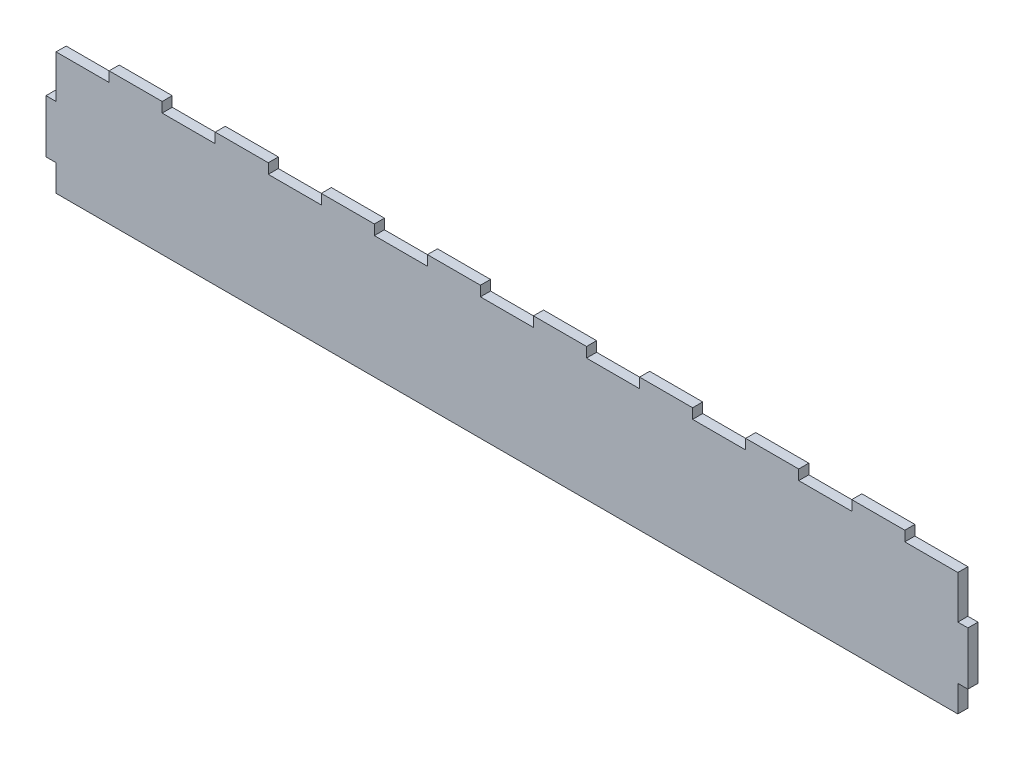
SolidWorks part; units mm, degrees
material "1060 Alloy"
ref_plane "Front Plane" through (0, 0, 0) normal (0, 0, 1) x (1, 0, 0)
ref_plane "Top Plane" through (0, 0, 0) normal (0, 1, 0) x (1, 0, 0)
ref_plane "Right Plane" through (0, 0, 0) normal (1, 0, 0) x (0, 0, -1)
sketch "Sketch2" plane through (0, 0, 0) normal (0, 0, 1) x (1, 0, 0)
  line L0 (0, 101.6) -> (0, 127)
  line L1 (0, 0) -> (431.8, 0)
  line L2 (0, 0) -> (0, 25.4)
  line L3 (0, 127) -> (431.8, 127)
  line L4 (431.8, 50.8) -> (431.8, 76.2)
  line L5 (0, 101.6) -> (-4.826, 101.6)
  line L6 (50.8, 122.174) -> (76.2, 122.174)
  line L7 (0, 76.2) -> (-4.826, 76.2)
  line L8 (-4.826, 101.6) -> (-4.826, 76.2)
  line L9 (0, 50.8) -> (-4.826, 50.8)
  line L10 (406.4, 122.174) -> (431.8, 122.174)
  line L11 (0, 25.4) -> (-4.826, 25.4)
  line L12 (-4.826, 50.8) -> (-4.826, 25.4)
  line L13 (0, 50.8) -> (0, 76.2)
  line L14 (215.9, 127) -> (215.9, 0) construction
  line L15 (406.4, 127) -> (406.4, 122.174)
  line L16 (0, 127) -> (25.4, 127)
  line L17 (0, 127) -> (0, 122.174)
  line L18 (0, 122.174) -> (25.4, 122.174)
  line L19 (25.4, 127) -> (25.4, 122.174)
  line L20 (50.8, 127) -> (50.8, 122.174)
  line L21 (76.2, 127) -> (76.2, 122.174)
  line L22 (101.6, 122.174) -> (127, 122.174)
  line L23 (101.6, 127) -> (101.6, 122.174)
  line L24 (127, 127) -> (127, 122.174)
  line L25 (152.4, 122.174) -> (177.8, 122.174)
  line L26 (152.4, 127) -> (152.4, 122.174)
  line L27 (177.8, 127) -> (177.8, 122.174)
  line L28 (203.2, 122.174) -> (228.6, 122.174)
  line L29 (203.2, 127) -> (203.2, 122.174)
  line L30 (228.6, 127) -> (228.6, 122.174)
  line L31 (254, 122.174) -> (279.4, 122.174)
  line L32 (254, 127) -> (254, 122.174)
  line L33 (279.4, 127) -> (279.4, 122.174)
  line L34 (304.8, 122.174) -> (330.2, 122.174)
  line L35 (304.8, 127) -> (304.8, 122.174)
  line L36 (330.2, 127) -> (330.2, 122.174)
  line L37 (355.6, 122.174) -> (381, 122.174)
  line L38 (355.6, 127) -> (355.6, 122.174)
  line L39 (381, 127) -> (381, 122.174)
  line L40 (436.626, 50.8) -> (436.626, 25.4)
  line L41 (431.8, 25.4) -> (436.626, 25.4)
  line L42 (431.8, 50.8) -> (436.626, 50.8)
  line L43 (436.626, 101.6) -> (436.626, 76.2)
  line L44 (431.8, 76.2) -> (436.626, 76.2)
  line L45 (431.8, 101.6) -> (436.626, 101.6)
  line L46 (431.8, 0) -> (431.8, 25.4)
  line L47 (431.8, 101.6) -> (431.8, 127)
  line L48 (431.8, 127) -> (431.8, 122.174)
  dimension "D1" = 127
  dimension "D2" = 431.8
  dimension "D3" = 4.826
  dimension "D5" = 25.4
  dimension "D6" = 4.826
  dimension "D7" = 9
extrude "Boss-Extrude1" add sketch "Sketch2" along normal blind 4.826 contours L14 L3 L27 L25 L26 L24 L22 L23 L21 L6 L20 L19 L18 L17 L0 L5 L8 L7 L13 L9 L12 L11 L2 L1 | L3 L14 L1 L46 L41 L40 L42 L4 L44 L43 L45 L47 L39 L37 L38 L36 L34 L35 L33 L31 L32 L30 L28 L29
sketch "Sketch3" plane through (0, 0, 0) normal (0, 0, -1) x (-1, 0, 0)
  line L0 (-431.8, 50.8) -> (-431.8, 76.2) construction
  line L1 (4.826, 0) -> (-436.626, 0)
  line L2 (4.826, 0) -> (4.826, 63.5)
  line L3 (4.826, 63.5) -> (-436.626, 63.5)
  line L4 (-436.626, 0) -> (-436.626, 63.5)
  line L5 (-436.626, 50.8) -> (-436.626, 25.4) construction
  line L6 (4.826, 50.8) -> (4.826, 25.4) construction
  line L7 (0, 0) -> (-431.8, 0) construction
  point P4 (-431.8, 63.5)
extrude "Cut-Extrude1" cut sketch "Sketch3" against normal through all
equation "\"w\"= .19"
equation "\"D3@Sketch2\"=\"w\""
equation "\"D6@Sketch2\"=\"w\""
equation "\"D1@Boss-Extrude1\"=\"w\""
